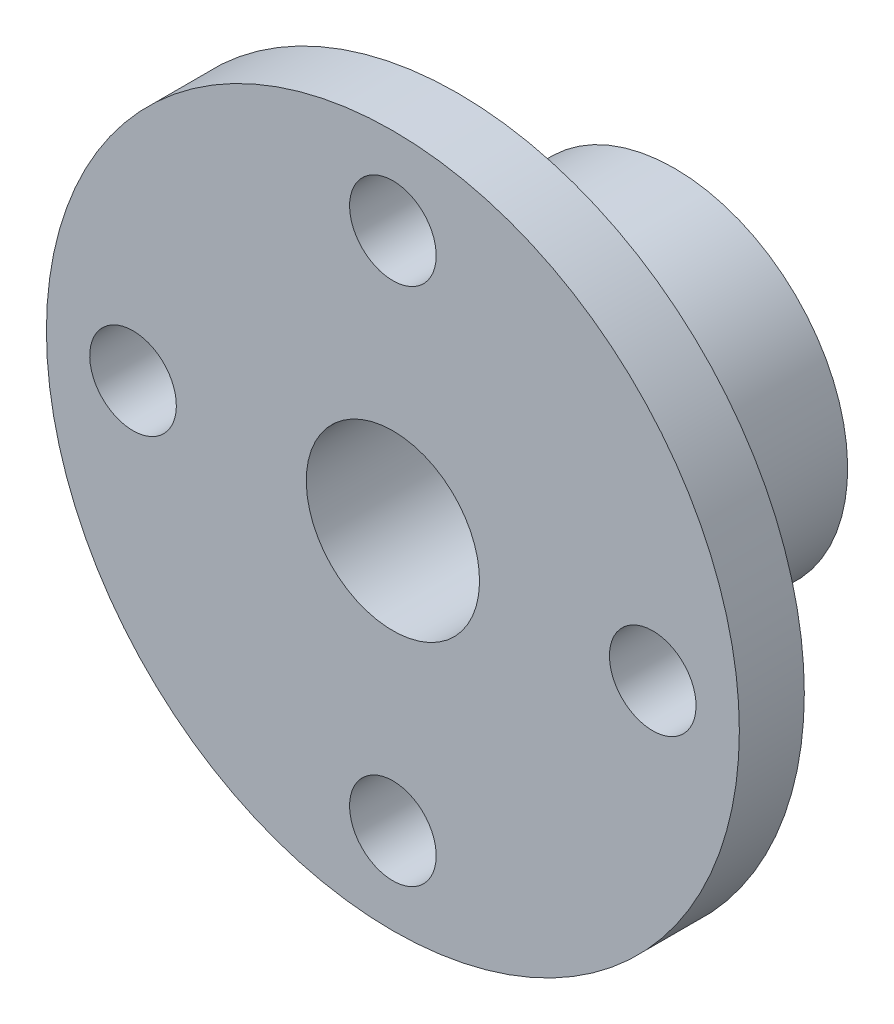
SolidWorks part; units mm, degrees
ref_plane "Front Plane" through (0, 0, 0) normal (0, 0, 1) x (1, 0, 0)
ref_plane "Top Plane" through (0, 0, 0) normal (0, 1, 0) x (1, 0, 0)
ref_plane "Right Plane" through (0, 0, 0) normal (1, 0, 0) x (0, 0, -1)
sketch "Sketch1" plane through (0, 0, 0) normal (0, 1, 0) x (1, 0, 0)
  line L0 (0, 0) -> (12, 0) construction
  circle A0 centre (0, 0) radius 4
  circle A1 centre (0, 0) radius 12 construction
  circle A2 centre (0, 0) radius 16
  circle A3 centre (12, 0) radius 2
  circle A4 centre (0, 0) radius 12 construction
  circle A5 centre (0, -12) radius 2
  circle A6 centre (0, 0) radius 12 construction
  circle A7 centre (-12, 0) radius 2
  circle A8 centre (0, 0) radius 12 construction
  circle A9 centre (0, 12) radius 2
  point P19 (0, 0)
  dimension "D1" = 8
  dimension "D2" = 24
  dimension "D3" = 32
  dimension "D4" = 4
  dimension "D5" = 4
extrude "Boss-Extrude1" add sketch "Sketch1" along normal blind 3
sketch "Sketch2" plane through (0, 0, 0) normal (0, 1, 0) x (1, 0, 0)
  circle A0 centre (0, 0) radius 8
  circle A1 centre (0, 0) radius 4
  dimension "D1" = 16
  dimension "D2" = 8
extrude "Boss-Extrude2" add sketch "Sketch2" along normal blind 13
move or copy body "Body-Move/Copy1" bodies to move or copy 102 copy no rotation origin (0, 6.5, 0) rotation axis (-1, 0, 0) rotation angle 90
